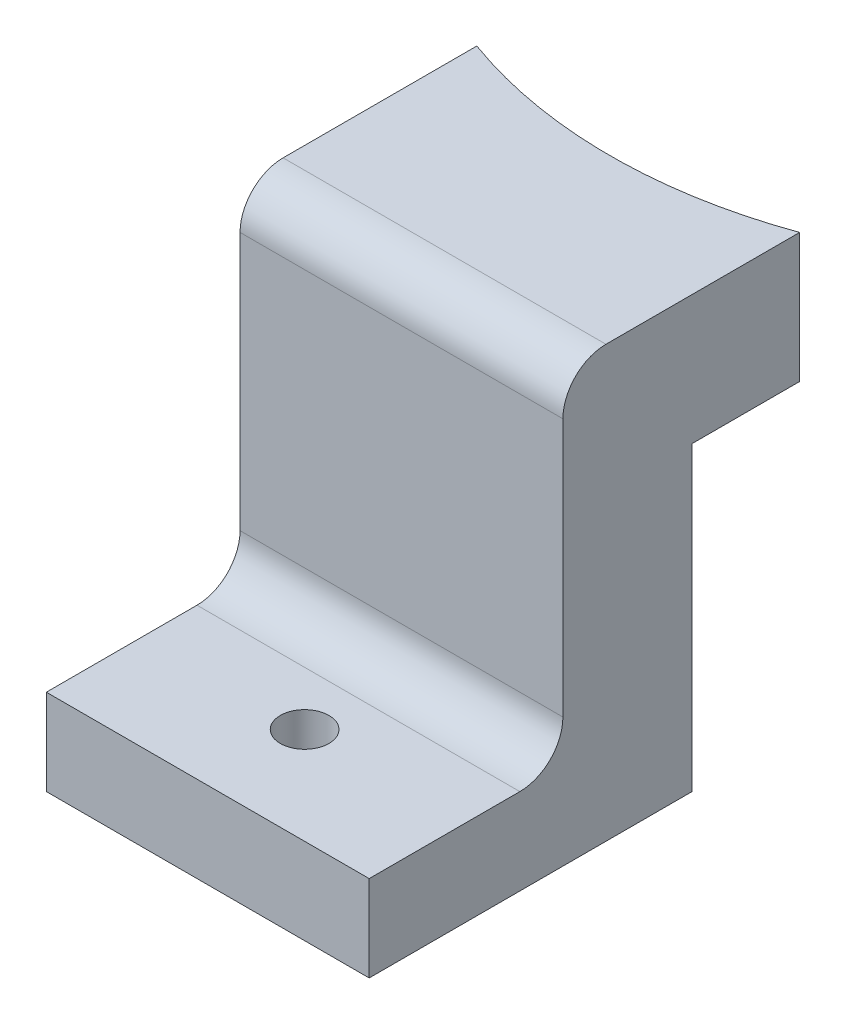
SolidWorks part; units mm, degrees
material "6061 Alloy"
ref_plane "Front Plane" through (0, 0, 0) normal (0, 0, 1) x (1, 0, 0)
ref_plane "Top Plane" through (0, 0, 0) normal (0, 1, 0) x (1, 0, 0)
ref_plane "Right Plane" through (0, 0, 0) normal (1, 0, 0) x (0, 0, -1)
sketch "Sketch1" plane through (0, 0, 0) normal (0, 1, 0) x (1, 0, 0)
  line L0 (7.5, 5) -> (-7.5, -5) construction
  line L1 (-7.5, 5) -> (7.5, 5)
  line L2 (-7.5, 5) -> (-7.5, -5)
  line L3 (-7.5, -5) -> (7.5, -5)
  line L4 (7.5, 5) -> (7.5, -5)
  line L5 (-7.5, 5) -> (7.5, -5) construction
  point P2 (0, 0)
  dimension "D1" = 15
  dimension "D2" = 10
extrude "Boss-Extrude1" add sketch "Sketch1" along normal blind 6
sketch "Sketch2" plane through (0, 6, 0) normal (0, 1, 0) x (1, 0, 0)
  circle A0 centre (0, 25.6821) radius 22
  dimension "D1" = 44
extrude "Cut-Extrude1" cut sketch "Sketch2" against normal blind 9
sketch "Sketch3" plane through (0, 6, 0) normal (0, 1, 0) x (1, 0, 0)
  line L0 (-7.5, 5) -> (-7.5, -5) construction
  line L1 (-7.5, 0) -> (7.5, 0)
  line L2 (-7.5, 0) -> (-7.5, -6)
  line L3 (-7.5, -6) -> (7.5, -6)
  line L4 (7.5, 0) -> (7.5, -6)
  line L5 (-7.5, -5) -> (7.5, -5) construction
  line L6 (7.5, -5) -> (7.5, 5) construction
  dimension "D1" = 5
  dimension "D2" = 0
  dimension "D3" = 15
  dimension "D4" = 6
extrude "Boss-Extrude2" add sketch "Sketch3" against normal blind 20
sketch "Sketch4" plane through (0, 0, 6) normal (0, 0, 1) x (1, 0, 0)
  line L0 (-7.5, -14) -> (7.5, -14) construction
  line L1 (-7.5, -10) -> (7.5, -10)
  line L2 (-7.5, -10) -> (-7.5, -14)
  line L3 (-7.5, -14) -> (7.5, -14)
  line L4 (7.5, -10) -> (7.5, -14)
  line L5 (7.5, -14) -> (7.5, 6) construction
  line L6 (-7.5, -14) -> (-7.5, 6) construction
  dimension "D1" = 4
  dimension "D3" = 0
extrude "Boss-Extrude3" add sketch "Sketch4" along normal blind 9
sketch "Sketch9" plane through (0, -14, 0) normal (0, -1, 0) x (1, 0, 0)
  line L0 (0, 15) -> (0, 0) construction
  line L1 (-7.5, 15) -> (7.5, 15) construction
  line L2 (7.5, 0) -> (-7.5, 0) construction
  line L3 (-7.5, 10.5) -> (7.5, 10.5) construction
  line L4 (-7.5, 0) -> (-7.5, 15) construction
  line L5 (7.5, 15) -> (7.5, 0) construction
  point P12 (0, 10.5)
  dimension "D1" = 4.5
hole_wizard "#4-40 Tapped Hole2" positions "Sketch10" profile "Sketch11" tap size "#4-40" standard "ANSI Inch"
sketch "Sketch10" plane through (0, -14, 0) normal (0, -1, 0) x (-1, 0, 0)
  point P0 (0, -10.5)
sketch "Sketch11" plane through (0, -14, 10.5) normal (1, 0, 0) x (0, 0, -1)
  line L0 (0, 0) -> (0, 8.2792)
  line L1 (0, 8.2792) -> (1.1303, 7.6)
  line L2 (1.1303, 7.6) -> (1.1303, 0)
  line L5 (1.1303, 0) -> (0, 0)
  line L10 (0, 8.2792) -> (-1.1303, 7.6) construction
  line L11 (0, -6.35) -> (0, 107.95) construction
  dimension "Tap Drill Dia." = 2.2606
  dimension "Tap Drill Depth" = 7.6
  dimension "Drill Angle" = 118
cosmetic thread "Hole Thread2" parameters "D1"=5.69, "D2"=2.8448
fillet "Fillet2" radius 2 2 edges at (0, -10, 6) (0, 6, 6)
